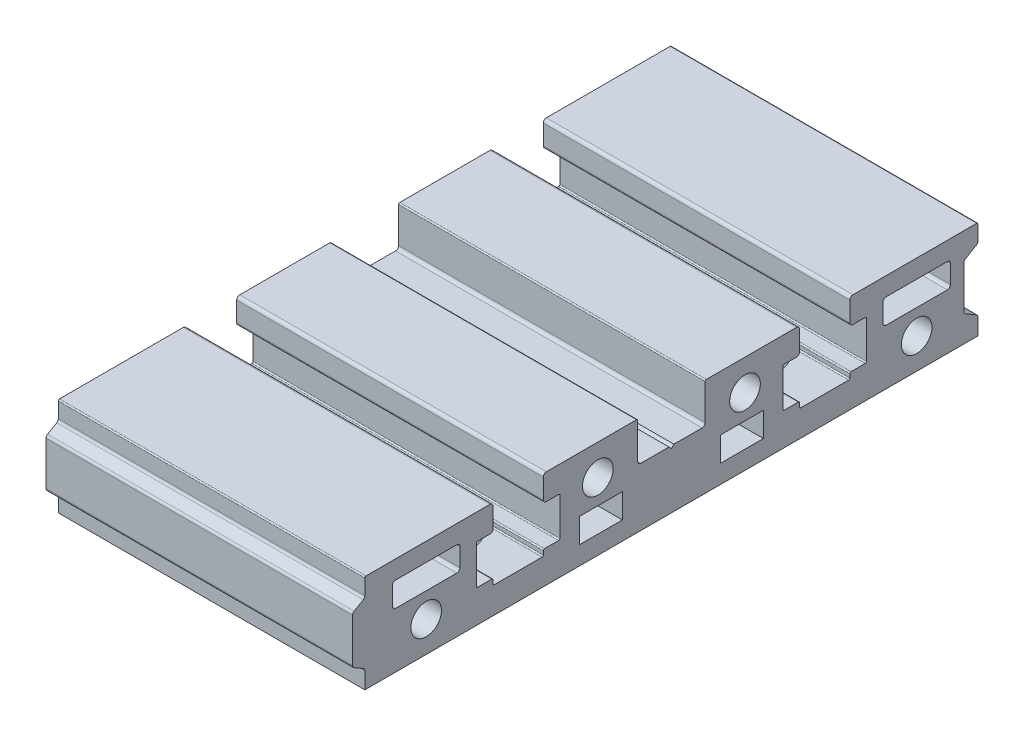
SolidWorks part; units mm, degrees
material "1060 Сплав"
ref_plane "Спереди" through (0, 0, 0) normal (0, 0, 1) x (1, 0, 0)
ref_plane "Сверху" through (0, 0, 0) normal (0, 1, 0) x (1, 0, 0)
ref_plane "Сбоку" through (0, 0, 0) normal (1, 0, 0) x (0, 0, -1)
sketch "Эскиз1" plane through (0, 0, 0) normal (1, 0, 0) x (0, 0, -1)
  line L0 (0, 0) -> (0, 16) construction
  line L1 (-5.5, 15.8) -> (-5.5, 10)
  line L2 (-5, 9.5) -> (-0.4, 9.5)
  line L3 (-0.4, 9.5) -> (0, 9.1)
  line L4 (-5.7, 16) -> (-20.4, 16)
  line L5 (-25, 16) -> (-25, 0) construction
  line L6 (-20.9, 15.5) -> (-20.9, 12.3)
  line L7 (-20.4, 11.8) -> (-18.4, 11.8)
  line L8 (-18.2, 11.6) -> (-18.2, 5.5)
  line L9 (-18.4, 5.3) -> (-20.7, 5.3)
  line L10 (-20.9, 5.1) -> (-20.9, 4.5)
  line L11 (-21.1, 4.3) -> (-28.9, 4.3)
  line L12 (-12, 16) -> (-12, 0) construction
  line L13 (-29.1, 5.1) -> (-29.1, 4.5)
  line L14 (-15, 7) -> (-8, 7)
  line L15 (-15, 7) -> (-15, 3)
  line L16 (-15, 3) -> (-8, 3)
  line L17 (-8, 7) -> (-8, 3)
  line L18 (-31.6, 5.3) -> (-29.3, 5.3)
  line L19 (-31.8, 11.6) -> (-31.8, 5.5)
  line L20 (-29.6, 11.8) -> (-31.6, 11.8)
  line L21 (-29.1, 15.5) -> (-29.1, 12.3)
  line L22 (12, 16) -> (12, 0) construction
  line L23 (25, 16) -> (25, 0) construction
  line L24 (29.1, 15.5) -> (29.1, 12.3)
  line L25 (29.6, 11.8) -> (31.6, 11.8)
  line L26 (31.8, 11.6) -> (31.8, 5.5)
  line L27 (31.6, 5.3) -> (29.3, 5.3)
  line L28 (8, 7) -> (8, 3)
  line L29 (15, 3) -> (8, 3)
  line L30 (15, 7) -> (15, 3)
  line L31 (15, 7) -> (8, 7)
  line L32 (29.1, 5.1) -> (29.1, 4.5)
  line L33 (21.1, 4.3) -> (28.9, 4.3)
  line L34 (20.9, 5.1) -> (20.9, 4.5)
  line L35 (18.4, 5.3) -> (20.7, 5.3)
  line L36 (18.2, 11.6) -> (18.2, 5.5)
  line L37 (20.4, 11.8) -> (18.4, 11.8)
  line L38 (20.9, 15.5) -> (20.9, 12.3)
  line L39 (5.7, 16) -> (20.4, 16)
  line L40 (0.4, 9.5) -> (0, 9.1)
  line L41 (5, 9.5) -> (0.4, 9.5)
  line L42 (5.5, 15.8) -> (5.5, 10)
  line L43 (-29.6, 16) -> (-49.8, 16)
  line L44 (29.6, 16) -> (49.8, 16)
  line L45 (-50, 0) -> (50, 0)
  line L46 (-40, 0) -> (-40, 16) construction
  line L47 (-50, 15.8) -> (-50, 13.2887)
  line L48 (-45, 13) -> (-35, 13)
  line L49 (-45.5, 12.5) -> (-45.5, 9.5)
  line L50 (-45, 9) -> (-35, 9)
  line L51 (-34.5, 12.5) -> (-34.5, 9.5)
  line L52 (-45.5, 13) -> (-34.5, 9) construction
  line L53 (-45.5, 9) -> (-34.5, 13) construction
  line L54 (-50.25, 12.8557) -> (-51.75, 11.9896)
  line L55 (-52, 11.5566) -> (-52, 4.4434)
  line L56 (-51.75, 4.0104) -> (-50.25, 3.1443)
  line L57 (-50, 2.7113) -> (-50, 0)
  line L58 (-50, 3) -> (-52, 3) construction
  line L59 (45.5, 9) -> (34.5, 13) construction
  line L60 (45.5, 13) -> (34.5, 9) construction
  line L61 (34.5, 12.5) -> (34.5, 9.5)
  line L62 (45, 9) -> (35, 9)
  line L63 (45.5, 12.5) -> (45.5, 9.5)
  line L64 (45, 13) -> (35, 13)
  line L65 (50, 15.8) -> (50, 13.3787)
  line L66 (49.75, 12.9457) -> (47.95, 11.9064)
  line L67 (47.7, 11.4734) -> (47.7, 4.5666)
  line L68 (47.95, 4.1336) -> (49.75, 3.0943)
  line L69 (50, 2.6613) -> (50, 0)
  line L70 (47.7, 11.7621) -> (50, 11.7621) construction
  arc A0 (-5.5, 10) -> (-5, 9.5) centre (-5, 10) ccw
  arc A1 (-5.5, 15.8) -> (-5.7, 16) centre (-5.7, 15.8) ccw
  circle A2 centre (-12, 11) radius 2.5
  arc A3 (-18.4, 11.8) -> (-18.2, 11.6) centre (-18.4, 11.6) cw
  arc A4 (-18.2, 5.5) -> (-18.4, 5.3) centre (-18.4, 5.5) cw
  arc A5 (-20.9, 4.5) -> (-21.1, 4.3) centre (-21.1, 4.5) cw
  arc A6 (-20.7, 5.3) -> (-20.9, 5.1) centre (-20.7, 5.1) ccw
  arc A7 (-20.4, 16) -> (-20.9, 15.5) centre (-20.4, 15.5) ccw
  arc A8 (-20.9, 12.3) -> (-20.4, 11.8) centre (-20.4, 12.3) ccw
  arc A9 (-29.1, 12.3) -> (-29.6, 11.8) centre (-29.6, 12.3) cw
  arc A10 (-29.6, 16) -> (-29.1, 15.5) centre (-29.6, 15.5) cw
  arc A11 (-29.3, 5.3) -> (-29.1, 5.1) centre (-29.3, 5.1) cw
  arc A12 (-29.1, 4.5) -> (-28.9, 4.3) centre (-28.9, 4.5) ccw
  arc A13 (-31.8, 5.5) -> (-31.6, 5.3) centre (-31.6, 5.5) ccw
  arc A14 (-31.6, 11.8) -> (-31.8, 11.6) centre (-31.6, 11.6) ccw
  arc A15 (31.6, 11.8) -> (31.8, 11.6) centre (31.6, 11.6) cw
  arc A16 (31.8, 5.5) -> (31.6, 5.3) centre (31.6, 5.5) cw
  arc A17 (29.1, 4.5) -> (28.9, 4.3) centre (28.9, 4.5) cw
  arc A18 (29.3, 5.3) -> (29.1, 5.1) centre (29.3, 5.1) ccw
  arc A19 (29.6, 16) -> (29.1, 15.5) centre (29.6, 15.5) ccw
  arc A20 (29.1, 12.3) -> (29.6, 11.8) centre (29.6, 12.3) ccw
  arc A21 (20.9, 12.3) -> (20.4, 11.8) centre (20.4, 12.3) cw
  arc A22 (20.4, 16) -> (20.9, 15.5) centre (20.4, 15.5) cw
  arc A23 (20.7, 5.3) -> (20.9, 5.1) centre (20.7, 5.1) cw
  arc A24 (20.9, 4.5) -> (21.1, 4.3) centre (21.1, 4.5) ccw
  arc A25 (18.2, 5.5) -> (18.4, 5.3) centre (18.4, 5.5) ccw
  arc A26 (18.4, 11.8) -> (18.2, 11.6) centre (18.4, 11.6) ccw
  circle A27 centre (12, 11) radius 2.5
  arc A28 (5.5, 15.8) -> (5.7, 16) centre (5.7, 15.8) cw
  arc A29 (5.5, 10) -> (5, 9.5) centre (5, 10) cw
  circle A30 centre (-40, 5) radius 2.5
  arc A31 (-35, 9) -> (-34.5, 9.5) centre (-35, 9.5) ccw
  arc A32 (-35, 13) -> (-34.5, 12.5) centre (-35, 12.5) cw
  arc A33 (-45.5, 9.5) -> (-45, 9) centre (-45, 9.5) ccw
  arc A34 (-45, 13) -> (-45.5, 12.5) centre (-45, 12.5) ccw
  arc A35 (-50.25, 3.1443) -> (-50, 2.7113) centre (-50.5, 2.7113) cw
  arc A36 (-52, 4.4434) -> (-51.75, 4.0104) centre (-51.5, 4.4434) ccw
  arc A37 (-51.75, 11.9896) -> (-52, 11.5566) centre (-51.5, 11.5566) ccw
  arc A38 (-50, 13.2887) -> (-50.25, 12.8557) centre (-50.5, 13.2887) cw
  arc A39 (45, 13) -> (45.5, 12.5) centre (45, 12.5) cw
  arc A40 (45.5, 9.5) -> (45, 9) centre (45, 9.5) cw
  arc A41 (35, 13) -> (34.5, 12.5) centre (35, 12.5) ccw
  arc A42 (35, 9) -> (34.5, 9.5) centre (35, 9.5) cw
  circle A43 centre (40, 5) radius 2.5
  arc A44 (-49.8, 16) -> (-50, 15.8) centre (-49.8, 15.8) ccw
  arc A45 (49.8, 16) -> (50, 15.8) centre (49.8, 15.8) cw
  arc A46 (49.75, 3.0943) -> (50, 2.6613) centre (49.5, 2.6613) cw
  arc A47 (47.7, 4.5666) -> (47.95, 4.1336) centre (48.2, 4.5666) ccw
  arc A48 (47.95, 11.9064) -> (47.7, 11.4734) centre (48.2, 11.4734) ccw
  arc A49 (50, 13.3787) -> (49.75, 12.9457) centre (49.5, 13.3787) cw
  point P12 (-5.5, 16)
  point P21 (-29.1, 11.8)
  point P39 (-20.9, 16)
  point P42 (-20.9, 11.8)
  point P61 (-25, 4.3)
  point P62 (-29.1, 16)
  point P116 (29.1, 16)
  point P117 (25, 4.3)
  point P118 (20.9, 11.8)
  point P119 (20.9, 16)
  point P120 (29.1, 11.8)
  point P121 (5.5, 16)
  point P130 (-40, 11)
  point P161 (-50, 13)
  point P180 (40, 11)
  point P188 (-50, 16)
  point P191 (50, 16)
  point P194 (50, 2.95)
  point P202 (50, 13.09)
  dimension "D5" = 0.5
  dimension "D7" = 0.2
  dimension "D10" = 5
  dimension "D21" = 0.2
  dimension "D22" = 0.5
  dimension "D26" = 5
  dimension "D30" = 0.5
  dimension "D36" = 0.5
  dimension "D42" = 0.2
  dimension "D43" = 0.5
  dimension "D1" = 16
  dimension "D2" = 45
  dimension "D3" = 0.4
  dimension "D4" = 6.5
  dimension "D6" = 5.5
  dimension "D8" = 25
  dimension "D9" = 12
  dimension "D11" = 5
  dimension "D12" = 3
  dimension "D13" = 7
  dimension "D14" = 8
  dimension "D15" = 4
  dimension "D16" = 4.1
  dimension "D17" = 6.8
  dimension "D18" = 4.2
  dimension "D19" = 11.7
  dimension "D20" = 10.7
  dimension "D23" = 25
  dimension "D24" = 100
  dimension "D25" = 28
  dimension "D27" = 5
  dimension "D28" = 4
  dimension "D29" = 11
  dimension "D31" = 3
  dimension "D32" = 10
  dimension "D33" = 3
  dimension "D34" = 2
  dimension "D35" = 30
  dimension "D37" = 4.5
  dimension "D38" = 2.3
  dimension "D39" = 2.95
  dimension "D40" = 30
  dimension "D41" = 10.14
  dimension "D44" = 102
extrude "Бобышка-Вытянуть1" add sketch "Эскиз1" along normal blind 50
hole_wizard "Диаметр отверстия Ø6.0 (6)1" positions "Эскиз3" profile "Эскиз4" hole size "Ø6.0" standard "ГОСТ" end condition through all
sketch "Эскиз3" plane through (0, 4.3, 0) normal (0, 1, 0) x (1, 0, 0)
  line L0 (0, 28.9) -> (0, 21.1) construction
  line L1 (10, 25) -> (0, 25)
  line L3 (10, -25) -> (0, -25)
  line L4 (0, -21.1) -> (0, -28.9) construction
  line L6 (25, -21.1) -> (25, 16.2457) construction
  line L7 (50, -21.1) -> (0, -21.1) construction
  point P0 (10, 25)
  point P2 (10, -25)
  point P21 (40, -25)
  point P22 (40, 25)
  dimension "D1" = 10
sketch "Эскиз4" plane through (10, 4.3, -25) normal (1, 0, 0) x (0, 0, 1)
  line L0 (0, 0) -> (0, 4.3)
  line L1 (0, 4.3) -> (3, 4.3)
  line L2 (3, 4.3) -> (3, 0)
  line L5 (3, 0) -> (0, 0)
  line L11 (0, -6.35) -> (0, 107.95) construction
  dimension "Диаметр сквозного отверстия" = 6
  dimension "Глубина сквозного отверстия" = 4.3
